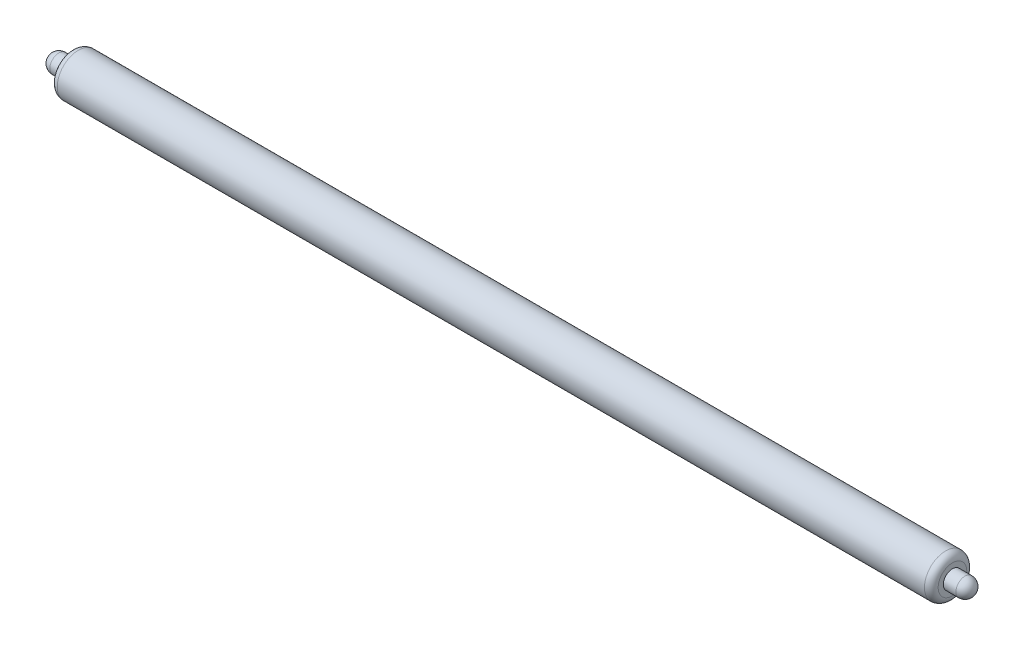
SolidWorks part; units mm, degrees
ref_plane "Plano frontal" through (0, 0, 0) normal (0, 0, 1) x (1, 0, 0)
ref_plane "Plano superior" through (0, 0, 0) normal (0, 1, 0) x (1, 0, 0)
ref_plane "Plano direito" through (0, 0, 0) normal (1, 0, 0) x (0, 0, -1)
sketch "Esboço1" plane through (0, 0, 0) normal (1, 0, 0) x (0, 0, -1)
  circle A0 centre (0, 0) radius 9.25
  dimension "D1" = 18.5
extrude "Ressalto-extrusão1" add sketch "Esboço1" along normal blind 385
sketch "Esboço2" plane through (0, 0, 0) normal (-1, 0, 0) x (0, 0, 1)
  circle A0 centre (0, 0) radius 4
  dimension "D1" = 8
extrude "Ressalto-extrusão2" add sketch "Esboço2" along normal blind 9.5
fillet "Filete1" radius 3 2 edges at (385, 0, -9.25) (0, 0, -9.25)
sketch "Esboço3" plane through (385, 0, 0) normal (1, 0, 0) x (0, 0, -1)
  circle A0 centre (0, 0) radius 4
  dimension "D1" = 8
extrude "Ressalto-extrusão3" add sketch "Esboço3" along normal blind 9.5
fillet "Filete2" radius 4 2 edges at (-9.5, 0, 4) (394.5, 0, -4)
